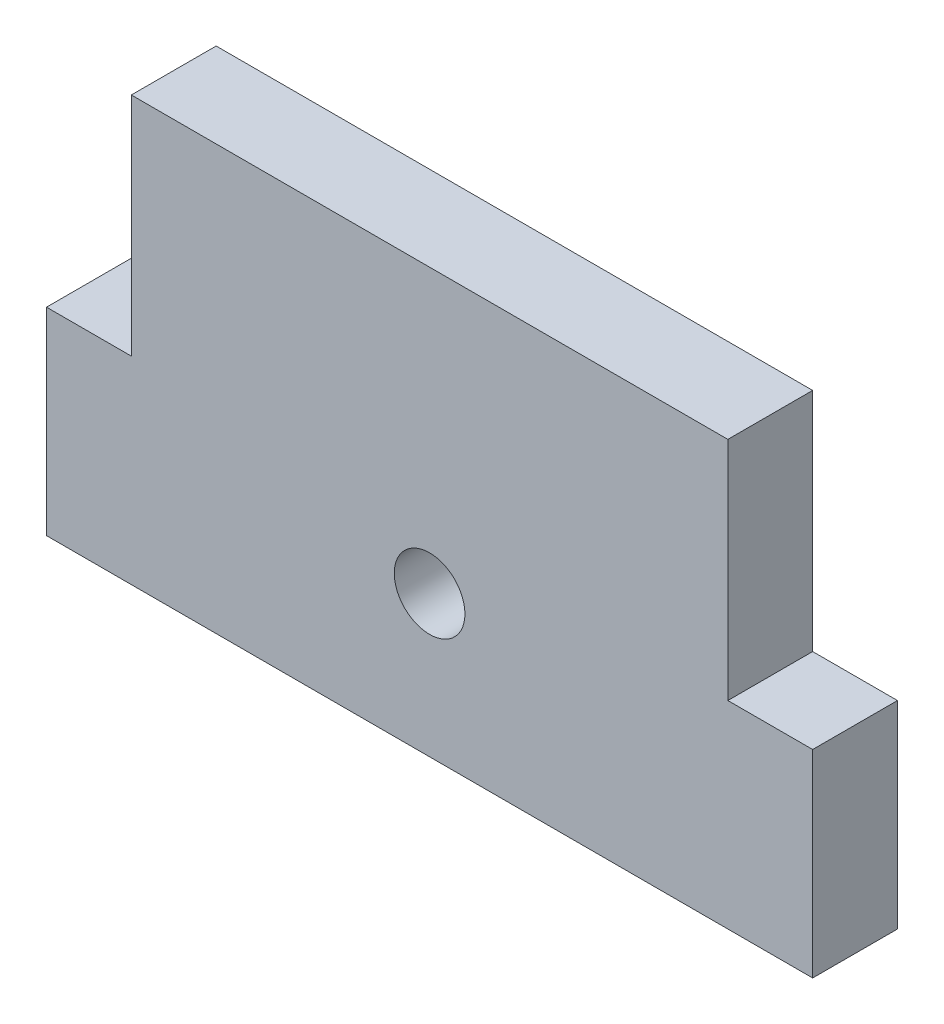
SolidWorks part; units mm, degrees
ref_plane "Front Plane" through (0, 0, 0) normal (0, 0, 1) x (1, 0, 0)
ref_plane "Top Plane" through (0, 0, 0) normal (0, 1, 0) x (1, 0, 0)
ref_plane "Right Plane" through (0, 0, 0) normal (1, 0, 0) x (0, 0, -1)
sketch "Sketch1" plane through (0, 0, 0) normal (0, 0, 1) x (1, 0, 0)
  line L1 (6, 30) -> (48.2, 30)
  line L2 (0, 14) -> (0, 0)
  line L3 (0, 0) -> (54.2, 0)
  line L4 (54.2, 14) -> (54.2, 0)
  line L7 (0, 14) -> (6, 14)
  line L8 (6, 30) -> (6, 14)
  line L11 (54.2, 14) -> (48.2, 14)
  line L12 (48.2, 30) -> (48.2, 14)
  circle A0 centre (27.1, 10) radius 2.5
  point P11 (27.1, 0)
  dimension "D8" = 5
  dimension "D1" = 30
  dimension "D2" = 42.2
  dimension "D3" = 16
  dimension "D4" = 6
  dimension "D5" = 6
  dimension "D6" = 16
  dimension "D7" = 10
extrude "Boss-Extrude1" add sketch "Sketch1" along normal blind 6
